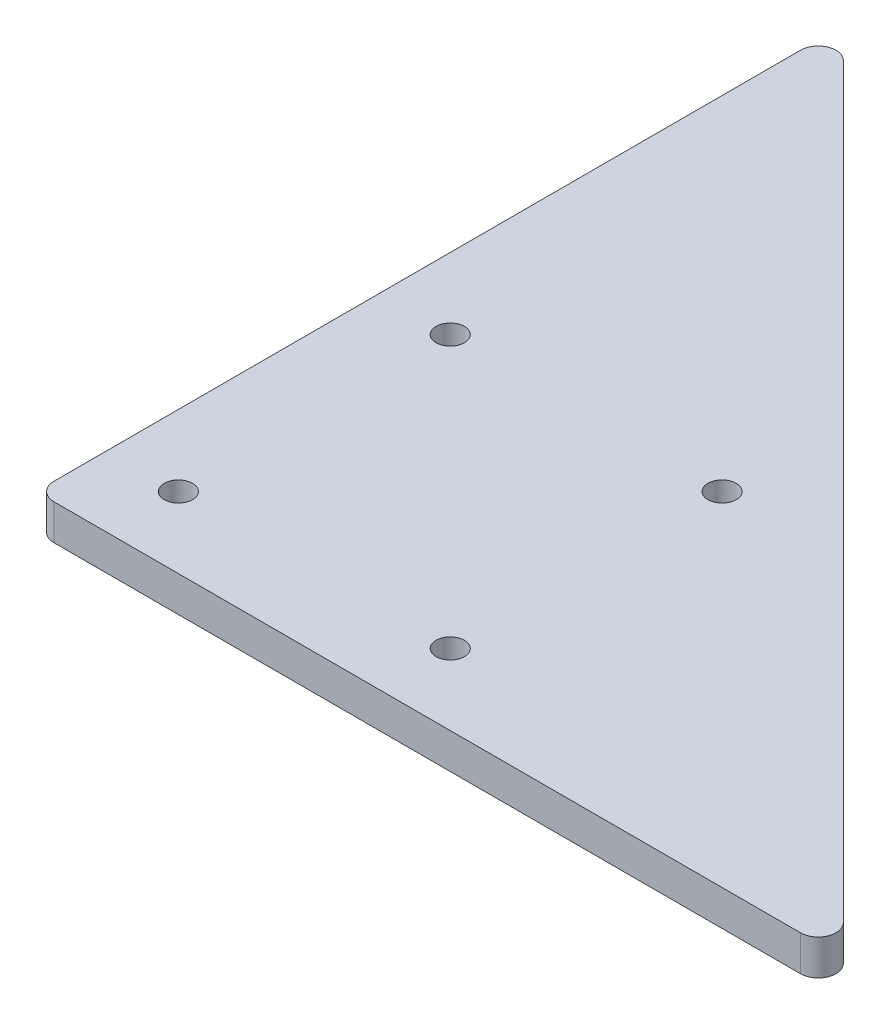
SolidWorks part; units mm, degrees
ref_plane "Front Plane" through (0, 0, 0) normal (0, 0, 1) x (1, 0, 0)
ref_plane "Top Plane" through (0, 0, 0) normal (0, 1, 0) x (1, 0, 0)
ref_plane "Right Plane" through (0, 0, 0) normal (1, 0, 0) x (0, 0, -1)
sketch "Sketch1" plane through (0, 0, 0) normal (0, 1, 0) x (1, 0, 0)
  line L0 (-35, 35) -> (-35, 45)
  line L1 (-35, 35) -> (35, 35) construction
  line L2 (-35, 35) -> (-35, -32)
  line L3 (-32, -35) -> (35, -35)
  line L4 (35, 35) -> (35, -35) construction
  line L5 (-35, 35) -> (35, -35) construction
  line L6 (-35, -35) -> (35, 35) construction
  line L7 (-35, 45) -> (27.5754, 36.0607)
  line L8 (35, -35) -> (45, -35)
  line L9 (45, -35) -> (36.0607, 27.5754)
  line L10 (45, -35) -> (94.2218, -35)
  line L11 (-35, -35) -> (1185, -35) construction
  line L12 (96.3431, -29.8787) -> (-29.8787, 96.3431)
  line L13 (-35, 1185) -> (-35, -35) construction
  line L14 (-35, 94.2218) -> (-35, 45)
  circle A0 centre (-22.981, 22.981) radius 2.4
  circle A1 centre (22.981, 22.981) radius 2.4
  circle A2 centre (22.981, -22.981) radius 2.4
  circle A3 centre (-22.981, -22.981) radius 2.4
  arc A4 (27.5754, 36.0607) -> (36.0607, 27.5754) centre (26.1612, 26.1612) cw
  arc A5 (-35, -32) -> (-32, -35) centre (-32, -32) ccw
  arc A6 (-29.8787, 96.3431) -> (-35, 94.2218) centre (-32, 94.2218) ccw
  arc A7 (94.2218, -35) -> (96.3431, -29.8787) centre (94.2218, -32) ccw
  point P0 (0, 0)
  point P11 (0, 0)
  point P14 (0, 0)
  point P17 (0, 0)
  point P20 (0, 0)
  point P34 (-35, 101.4645)
  point P37 (101.4645, -35)
  dimension "D3" = 4.8
  dimension "D7" = 10
  dimension "D9" = 3
  dimension "D11" = 3
  dimension "D1" = 70
  dimension "D2" = 70
  dimension "D4" = 65
  dimension "D6" = 80
  dimension "D8" = 32.5
  dimension "D10" = 45
  dimension "D5" = 4
extrude "Boss-Extrude1" add sketch "Sketch1" along normal blind 6 contours L2 A5 L3 L8 L9 A4 L7 L0 A0 A1 A2 A3 | L7 A4 L12 L14 | L12 A4 L9 L10
